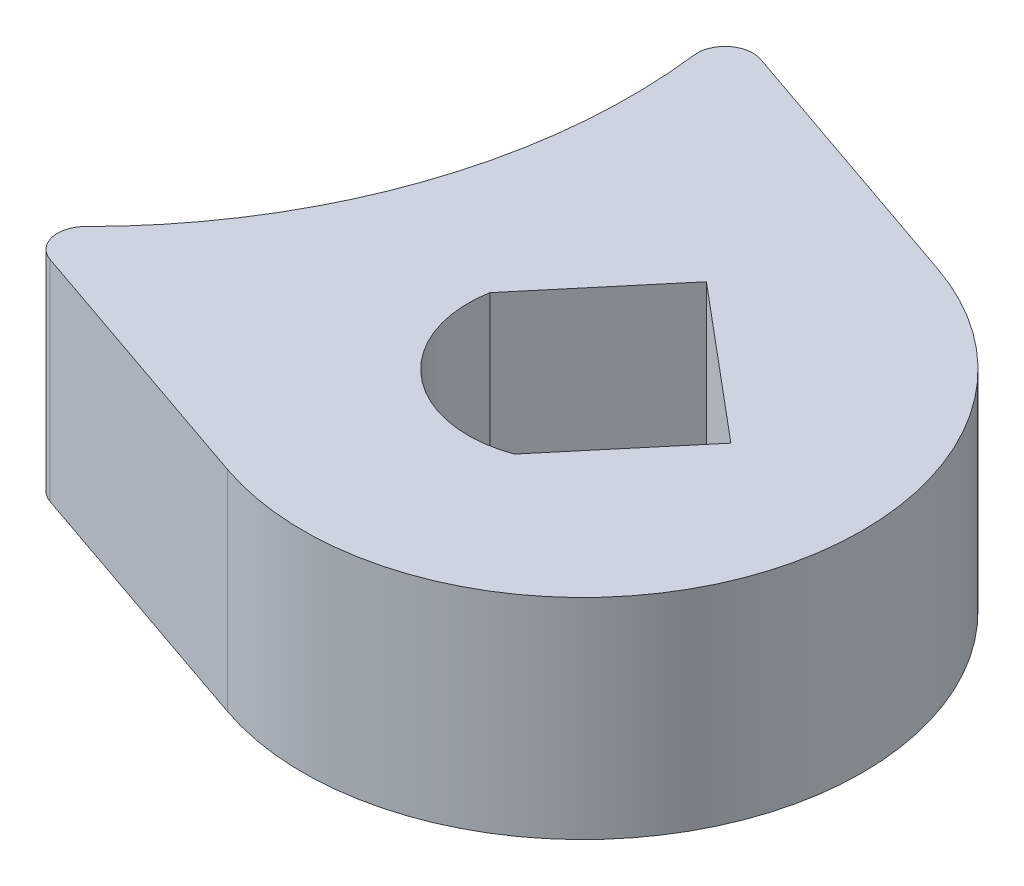
SolidWorks part; units mm, degrees
ref_plane "Front Plane" through (0, 0, 0) normal (0, 0, 1) x (1, 0, 0)
ref_plane "Top Plane" through (0, 0, 0) normal (0, 1, 0) x (1, 0, 0)
ref_plane "Right Plane" through (0, 0, 0) normal (1, 0, 0) x (0, 0, -1)
sketch "Sketch1" plane through (0, 0, 0) normal (0, 1, 0) x (1, 0, 0)
  line L3 (0, 0) -> (-47.3457, 0) construction
  line L4 (0, 0) -> (-6.692, -7.9752) construction
  line L5 (-1.2727, 12.5112) -> (12.5422, 0.9192)
  line L6 (12.5422, 0.9192) -> (3.5624, -9.7824)
  line L8 (-10.2524, 1.8096) -> (-1.2727, 12.5112)
  line L9 (-10.2524, 1.8096) -> (3.5624, -9.7824) construction
  line L10 (8.2682, 24.0166) -> (-20.351, 33.8693)
  line L11 (-20.351, 33.8693) -> (-36.8874, -14.1639) construction
  line L12 (-36.8874, -14.1639) -> (-8.2682, -24.0166)
  line L13 (0, 0) -> (-21.9875, 7.5696) construction
  arc A0 (-10.2524, 1.8096) -> (3.5624, -9.7824) centre (0, 0) ccw
  arc A1 (-8.2682, -24.0166) -> (8.2682, 24.0166) centre (0, 0) ccw
  arc A2 (-20.351, 33.8693) -> (-36.8874, -14.1639) centre (-68.7915, 23.6829) cw
  point P8 (5.6347, 6.7152)
  point P9 (-6.692, -7.9752)
  point P16 (-21.9875, 7.5696)
  dimension "D4" = 50.8
  dimension "D5" = 49.5
  dimension "D1" = 19.177
  dimension "D2" = 13.97
  dimension "D3" = 18.034
  dimension "D6" = 50
extrude "Boss-Extrude1" add sketch "Sketch1" along normal blind 19.05
fillet "Fillet2" radius 2.54 2 edges at (-36.8874, 9.525, 14.1639) (-20.351, 9.525, -33.8693)
